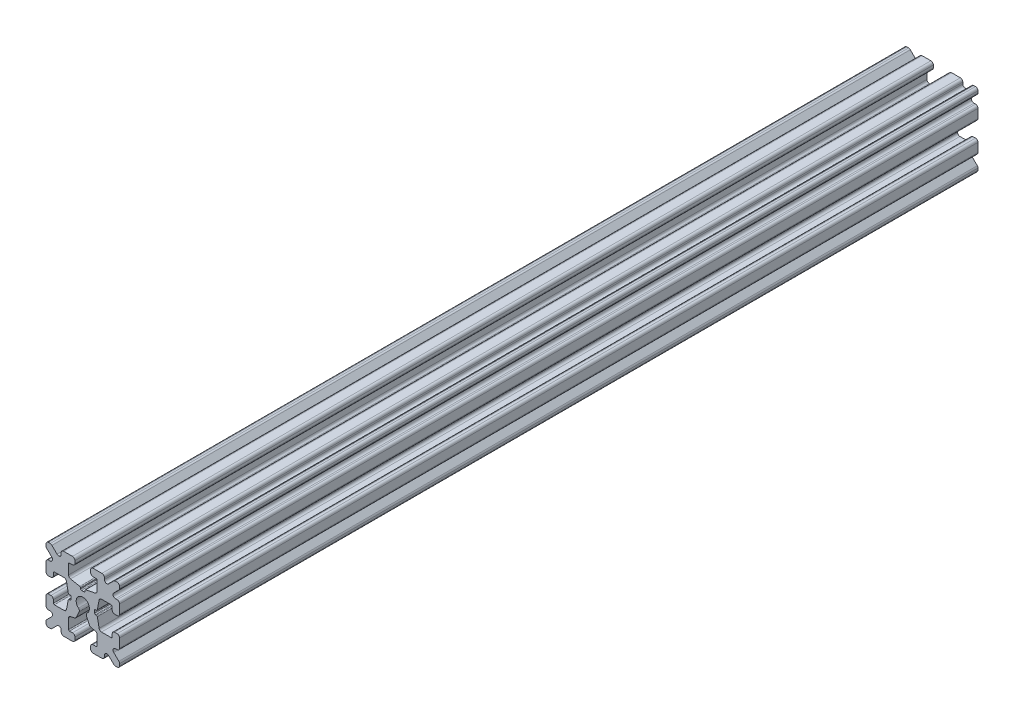
SolidWorks part; units mm, degrees
ref_plane "Front Plane" through (0, 0, 0) normal (0, 0, 1) x (1, 0, 0)
ref_plane "Top Plane" through (0, 0, 0) normal (0, 1, 0) x (1, 0, 0)
ref_plane "Right Plane" through (0, 0, 0) normal (1, 0, 0) x (0, 0, -1)
sketch "Sketch1" plane through (0, 0, 0) normal (0, 0, 1) x (1, 0, 0)
  line L1 (-7.5, -7.5) -> (7.5, -7.5)
  line L2 (-7.5, -7.5) -> (-7.5, 7.5)
  line L3 (-7.5, 7.5) -> (7.5, 7.5)
  line L4 (7.5, -7.5) -> (7.5, 7.5)
  line L5 (-7.5, -7.5) -> (7.5, 7.5) construction
  line L6 (-7.5, 7.5) -> (7.5, -7.5) construction
  circle A0 centre (0, 0) radius 1.35
  point P0 (0, 0)
  dimension "D2" = 2.7
  dimension "D1" = 15
extrude "Boss-Extrude1" add sketch "Sketch1" along normal mid plane 175
fillet "Fillet1" radius 0.5 4 edges at (7.5, -7.5, 0) (-7.5, -7.5, 0) (7.5, 7.5, 0) (-7.5, 7.5, 0)
sketch "Sketch2" plane through (0, 0, 87.5) normal (0, 0, 1) x (1, 0, 0)
  line L0 (-7.5, 7) -> (-7.5, -7) construction
  line L1 (-7.5, 1.6) -> (-6, 1.6)
  line L2 (-7.5, 1.6) -> (-7.5, -1.6)
  line L3 (-7.5, -1.6) -> (-6, -1.6)
  line L4 (-6, 1.6) -> (-6, 2.9)
  line L5 (0, 0) -> (-12.1036, 0) construction
  line L6 (-6, -2.9) -> (-3.4, -2.9)
  line L7 (0, 0) -> (-7, 7) construction
  line L8 (-6, 2.9) -> (-3.4, 2.9)
  line L9 (-3.4, -2.9) -> (-3.4, 2.9)
  line L10 (55, 0) -> (-55, 0) construction
  line L11 (-6, -2.9) -> (-6, -1.6)
  line L12 (2.9, 6) -> (1.6, 6)
  line L13 (2.9, 3.4) -> (-2.9, 3.4)
  line L14 (-2.9, 6) -> (-2.9, 3.4)
  line L15 (2.9, 6) -> (2.9, 3.4)
  line L16 (-1.6, 6) -> (-2.9, 6)
  line L17 (1.6, 7.5) -> (1.6, 6)
  line L18 (-1.6, 7.5) -> (1.6, 7.5)
  line L19 (-1.6, 7.5) -> (-1.6, 6)
  line L20 (-1.6, -7.5) -> (-1.6, -6)
  line L21 (-1.6, -7.5) -> (1.6, -7.5)
  line L22 (1.6, -7.5) -> (1.6, -6)
  line L23 (-1.6, -6) -> (-2.9, -6)
  line L24 (2.9, -6) -> (2.9, -3.4)
  line L25 (-2.9, -6) -> (-2.9, -3.4)
  line L26 (2.9, -3.4) -> (-2.9, -3.4)
  line L27 (2.9, -6) -> (1.6, -6)
  line L28 (6, -2.9) -> (6, -1.6)
  line L29 (3.4, -2.9) -> (3.4, 2.9)
  line L30 (6, 2.9) -> (3.4, 2.9)
  line L31 (6, -2.9) -> (3.4, -2.9)
  line L32 (6, 1.6) -> (6, 2.9)
  line L33 (7.5, -1.6) -> (6, -1.6)
  line L34 (7.5, 1.6) -> (7.5, -1.6)
  line L35 (7.5, 1.6) -> (6, 1.6)
  dimension "D1" = 3.2
  dimension "D2" = 5.8
  dimension "D3" = 1.5
  dimension "D4" = 2.6
extrude "Cut-Extrude1" cut sketch "Sketch2" against normal through all
sketch "Sketch4" plane through (0, 0, 87.5) normal (0, 0, 1) x (1, 0, 0)
  line L0 (-3.4, 2.9) -> (-2.85, 0)
  line L1 (55, 0) -> (-55, 0) construction
  line L2 (-2.85, 0) -> (-3.4, -2.9)
  line L3 (-3.4, -2.9) -> (-3.4, 2.9) construction
  line L4 (-3.4, 2.9) -> (-3.4, -2.9)
  line L5 (-2.9, 3.4) -> (0, 2.85)
  line L6 (0, 2.85) -> (2.9, 3.4)
  line L7 (2.9, 3.4) -> (-2.9, 3.4)
  line L8 (3.4, 2.9) -> (2.85, 0)
  line L9 (2.85, 0) -> (3.4, -2.9)
  line L10 (3.4, -2.9) -> (3.4, 2.9)
  line L11 (-2.9, -3.4) -> (0, -2.85)
  line L12 (0, -2.85) -> (2.9, -3.4)
  line L13 (2.9, -3.4) -> (-2.9, -3.4)
  circle A2 centre (0, 0) radius 2.85
  circle A3 centre (0, 0) radius 2.85 construction
  dimension "D1" = 1.5
extrude "Cut-Extrude3" cut sketch "Sketch4" against normal through all
fillet "Fillet3" radius 0.5 16 edges at (-6, -1.6, 0) (-7.5, -1.6, 0) (-6, 1.6, 0) (-7.5, 1.6, 0) (-1.6, -7.5, 0) (-1.6, -6, 0) (1.6, -7.5, 0) (1.6, -6, 0) (6, -1.6, 0) (7.5, -1.6, 0) (7.5, 1.6, 0) (6, 1.6, 0) (1.6, 7.5, 0) (1.6, 6, 0) (-1.6, 7.5, 0) (-1.6, 6, 0)
fillet "Fillet4" radius 0.5 8 edges at (-3.4, 2.9, 0) (-3.4, -2.9, 0) (2.9, -3.4, 0) (-2.9, -3.4, 0) (3.4, -2.9, 0) (3.4, 2.9, 0) (-2.9, 3.4, 0) (2.9, 3.4, 0)
fillet "Fillet5" radius 3 4 edges at (0, -2.85, 0) (2.85, 0, 0) (-2.85, 0, 0) (0, 2.85, 0)
fillet "Fillet6" radius 0.2 8 edges at (-2.9, -6, 0) (2.9, -6, 0) (6, -2.9, 0) (6, 2.9, 0) (2.9, 6, 0) (-2.9, 6, 0) (-6, -2.9, 0) (-6, 2.9, 0)
sketch "Sketch5" plane through (0, 0, 87.5) normal (0, 0, 1) x (1, 0, 0)
  line L0 (0, 0) -> (-7, 7) construction
  line L1 (-7.5, 6.4393) -> (-5.4607, 4.4)
  line L2 (-6.4393, 7.5) -> (-4.4, 5.4607)
  line L3 (-7.5, 4.4) -> (-5.4607, 4.4)
  line L4 (-3.8141, 2.9) -> (-5.8, 2.9) construction
  line L5 (0, 0) -> (-12.1819, 0) construction
  line L6 (-4.4, 7.5) -> (-4.4, 5.4607)
  line L7 (-2.9, 5.8) -> (-2.9, 3.8141) construction
  line L8 (-7.5, 6.4393) -> (-7.5, 4.4)
  line L9 (-7.5, 7) -> (-7.5, 2.1) construction
  line L10 (2.1, -7.5) -> (7, -7.5) construction
  line L11 (7.5, -7) -> (7.5, -2.1) construction
  line L12 (7, 7.5) -> (2.1, 7.5) construction
  line L13 (-2.1, 7.5) -> (-7, 7.5) construction
  line L14 (-4.4, 7.5) -> (-6.4393, 7.5)
  line L16 (55, 0) -> (-55, 0) construction
  line L17 (0, 0) -> (0, 10.993) construction
  line L18 (0, -54.6431) -> (0, 54.6431) construction
  line L20 (4.4, 7.5) -> (6.4393, 7.5)
  line L22 (7.5, 6.4393) -> (7.5, 4.4)
  line L23 (4.4, 7.5) -> (4.4, 5.4607)
  line L24 (7.5, 4.4) -> (5.4607, 4.4)
  line L25 (6.4393, 7.5) -> (4.4, 5.4607)
  line L26 (7.5, 6.4393) -> (5.4607, 4.4)
  line L27 (7.5, -6.4393) -> (5.4607, -4.4)
  line L28 (6.4393, -7.5) -> (4.4, -5.4607)
  line L29 (7.5, -4.4) -> (5.4607, -4.4)
  line L30 (4.4, -7.5) -> (4.4, -5.4607)
  line L31 (7.5, -6.4393) -> (7.5, -4.4)
  line L33 (4.4, -7.5) -> (6.4393, -7.5)
  line L36 (-4.4, -7.5) -> (-6.4393, -7.5)
  line L38 (-7.5, -6.4393) -> (-7.5, -4.4)
  line L39 (-4.4, -7.5) -> (-4.4, -5.4607)
  line L40 (-7.5, -4.4) -> (-5.4607, -4.4)
  line L41 (-6.4393, -7.5) -> (-4.4, -5.4607)
  line L42 (-7.5, -6.4393) -> (-5.4607, -4.4)
  dimension "D1" = 1.5
  dimension "D2" = 1.5
  dimension "D3" = 1.5
extrude "Cut-Extrude4" cut sketch "Sketch5" against normal through all
fillet "Fillet8" radius 0.5 24 edges at (-5.4607, 4.4, 0) (-7.5, 4.4, 0) (-5.4607, -4.4, 0) (-7.5, -4.4, 0) (-4.4, -7.5, 0) (-4.4, -5.4607, 0) (4.4, -7.5, 0) (4.4, -5.4607, 0) (5.4607, -4.4, 0) (7.5, -4.4, 0) (7.5, 4.4, 0) (5.4607, 4.4, 0) (4.4, 5.4607, 0) (4.4, 7.5, 0) (-4.4, 5.4607, 0) (-4.4, 7.5, 0) (-6.4393, 7.5, 0) (-7.5, 6.4393, 0) (6.4393, 7.5, 0) (7.5, 6.4393, 0) (6.4393, -7.5, 0) (7.5, -6.4393, 0) (-6.4393, -7.5, 0) (-7.5, -6.4393, 0)
sketch "Sketch6" plane through (0, 0, 87.5) normal (0, 0, 1) x (1, 0, 0)
  line L0 (0, 0) -> (0, 11.013) construction
  line L1 (0.559, 2.956) -> (2.1235, 2.956) construction
  line L2 (0, -54.6431) -> (0, 54.6431) construction
  line L3 (0, 0) -> (7, 7) construction
  line L4 (8.6552, 0.4445) -> (8.6552, -0.4445)
  line L5 (2.406, 0.4445) -> (8.6552, 0.4445)
  line L8 (2.406, -0.4445) -> (2.406, 0.4445)
  line L10 (8.6552, -0.4445) -> (2.406, -0.4445)
  line L11 (-8.6552, -0.4445) -> (-2.406, -0.4445)
  line L12 (-2.406, -0.4445) -> (-2.406, 0.4445)
  line L14 (-0.4445, 8.6552) -> (-0.4445, 2.406)
  line L15 (-0.4445, 2.406) -> (0.4445, 2.406)
  line L17 (0.4445, 2.406) -> (0.4445, 8.6552)
  line L18 (0.4445, 8.6552) -> (-0.4445, 8.6552)
  line L20 (-2.406, 0.4445) -> (-8.6552, 0.4445)
  line L21 (-8.6552, 0.4445) -> (-8.6552, -0.4445)
  point P7 (0, 2.5973)
  dimension "D3" = 0.55
  dimension "D1" = 0.889
extrude "Cut-Extrude5" cut sketch "Sketch6" against normal through all
sketch "Sketch7" plane through (0, 0, 87.5) normal (0, 0, 1) x (1, 0, 0)
  line L0 (0, 0) -> (-2.1533, -4.6178)
  line L1 (-2.1533, -4.6178) -> (2.1533, -4.6178)
  line L2 (2.1533, -4.6178) -> (0, 0)
  line L3 (0, 0) -> (0, -8.6832) construction
  line L4 (0, -54.6431) -> (0, 54.6431) construction
  dimension "D1" = 50
extrude "Cut-Extrude6" cut sketch "Sketch7" against normal through all
fillet "Fillet9" radius 0.5 4 edges at (0.5705, -1.2235, 0) (-0.5705, -1.2235, 0) (1.4579, -3.1265, 0) (-1.4579, -3.1265, 0)
fillet "Fillet10" radius 0.2 12 edges at (-2.406, 0.4445, 0) (-2.406, -0.4445, 0) (0.4445, 2.406, 0) (-0.4445, 2.406, 0) (2.406, 0.4445, 0) (2.406, -0.4445, 0) (-2.9366, -0.4445, 0) (-2.9366, 0.4445, 0) (2.9366, -0.4445, 0) (2.9366, 0.4445, 0) (0.4445, 2.9366, 0) (-0.4445, 2.9366, 0)
sketch "Sketch10" plane through (0, 0, 87.5) normal (0, 0, 1) x (1, 0, 0)
  line L0 (2.7, 6) -> (2.1, 6) construction
  line L1 (-2.75, 6) -> (2.75, 6)
  line L2 (-2.75, 6) -> (-2.75, 3.6)
  line L3 (-2.75, 3.6) -> (2.75, 3.6)
  line L4 (2.75, 6) -> (2.75, 3.6)
  line L5 (0, 0) -> (0, 8.8277) construction
  line L6 (-3.2398, 3.994) -> (-2.2083, 2.8606) construction
  line L7 (-3.878, 3.2131) -> (-3.2018, 2.4701) construction
  line L8 (-2.406, -0.2445) -> (-2.406, 0.2445) construction
  line L9 (-2.1, 7.5) -> (-3.9, 7.5) construction
  line L10 (-1.5, 7.5) -> (1.5, 7.5)
  line L11 (-1.5, 7.5) -> (-1.5, 3.5)
  line L12 (-1.5, 3.5) -> (1.5, 3.5)
  line L13 (1.5, 7.5) -> (1.5, 3.5)
  arc A1 (-3.3228, 2.4932) -> (-3.8141, 2.9) centre (-3.8141, 2.4) ccw construction
  arc A2 (-2.9, 3.8141) -> (-2.4932, 3.3228) centre (-2.4, 3.8141) ccw construction
  arc A3 (0.88, -1.0238) -> (-0.88, -1.0238) centre (0, 0) ccw construction
  point P19 (-1.35, 0)
  point P20 (-2.406, 0)
  dimension "D1" = 2.4
  dimension "D2" = 5.5
  dimension "D3" = 0.9976
  dimension "D4" = 3
  dimension "D5" = 4
sketch "Sketch11" plane through (0, 0, 87.5) normal (0, 0, 1) x (1, 0, 0)
  line L0 (-7.5, 7) -> (-7.5, 6.6464) construction
  line L1 (-7.5, 7.5) -> (7.5, 7.5) construction
  line L2 (-7.5, 7.5) -> (-7.5, -7.5) construction
  line L3 (-7.5, -7.5) -> (7.5, -7.5) construction
  line L4 (7.5, 7.5) -> (7.5, -7.5) construction
  line L5 (-7, -7.5) -> (-6.6464, -7.5) construction
  line L6 (7.5, 6.6464) -> (7.5, 7) construction
  line L7 (-2.1, 7.5) -> (-3.9, 7.5) construction
  point P0 (0, 7.5)
  point P1 (0, -7.5)
  point P2 (7.5, 0)
  point P3 (-7.5, 0)
sketch "Sketch12" plane through (0, 0, -87.5) normal (0, 0, -1) x (-1, 0, 0)
  line L1 (-7.5, -7.5) -> (7.5, -7.5) construction
  line L2 (-7.5, -7.5) -> (-7.5, 7.5) construction
  line L3 (-7.5, 7.5) -> (7.5, 7.5) construction
  line L4 (7.5, -7.5) -> (7.5, 7.5) construction
  point P4 (-7.5, 0)
  point P9 (0, -7.5)
  point P10 (7.5, 0)
  point P11 (0, 7.5)
sketch "Sketch13" plane through (0, -7.5, 0) normal (0, -1, 0) x (1, 0, 0)
  line L0 (0, 87.5) -> (0, -87.5) construction
  line L1 (-7.5, -87.5) -> (-7.5, 87.5) construction
  line L2 (7.5, 87.5) -> (7.5, -87.5) construction
sketch "Sketch14" plane through (-7.5, 0, 0) normal (-1, 0, 0) x (0, 0, 1)
  line L0 (87.5, 0) -> (-87.5, 0) construction
sketch "Sketch15" plane through (0, 7.5, 0) normal (0, 1, 0) x (1, 0, 0)
  line L0 (0, -87.5) -> (0, 87.5) construction
  line L1 (-7.5, -87.5) -> (7.5, -87.5) construction
  line L2 (-7.5, -87.5) -> (-7.5, 87.5) construction
  line L3 (7.5, 87.5) -> (7.5, -87.5) construction
sketch "Sketch16" plane through (7.5, 0, 0) normal (1, 0, 0) x (0, 0, -1)
  line L0 (-87.5, 0) -> (87.5, 0) construction
